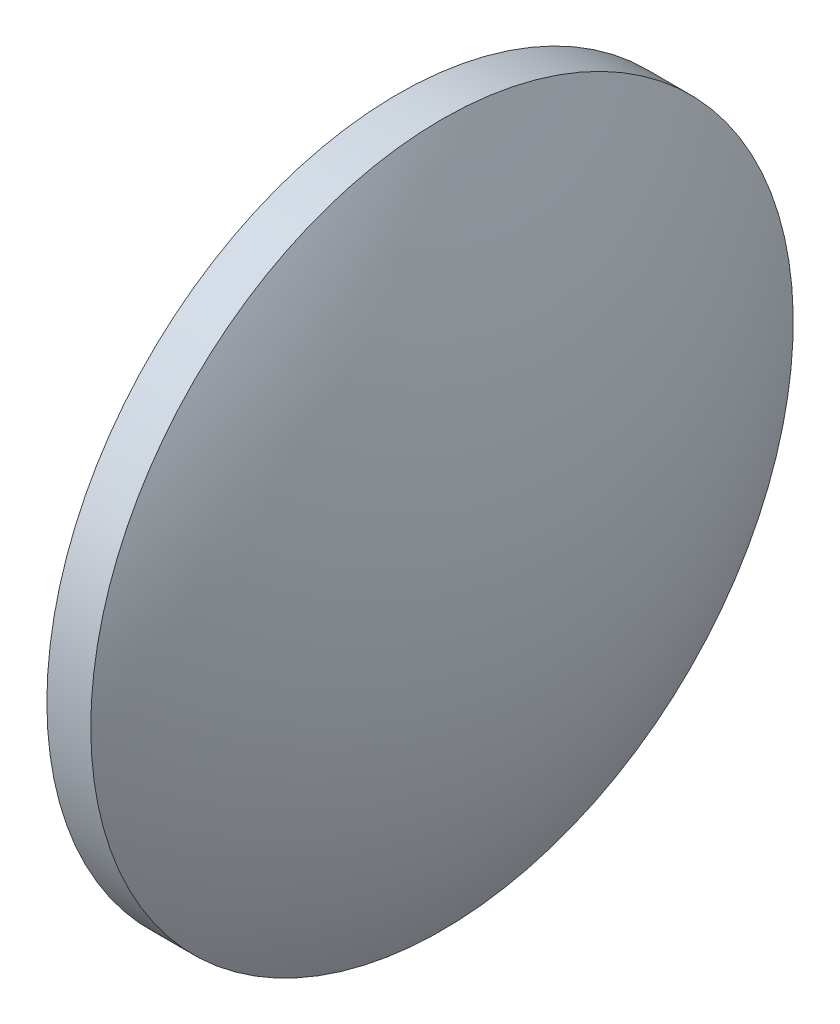
SolidWorks part; units mm, degrees
ref_plane "前视基准面" through (0, 0, 0) normal (0, 0, 1) x (1, 0, 0)
ref_plane "上视基准面" through (0, 0, 0) normal (0, 1, 0) x (1, 0, 0)
ref_plane "右视基准面" through (0, 0, 0) normal (1, 0, 0) x (0, 0, -1)
sketch "草图2" plane through (0, 0, 0) normal (0, 0, 1) x (1, 0, 0)
  line L0 (442.6491, 15.686) -> (461.8253, 15.686) construction
  line L1 (447.3437, 15.686) -> (447.3437, 35.686)
  line L2 (455.0137, 15.686) -> (447.3437, 15.686)
  line L5 (449.8437, 35.686) -> (447.3437, 35.686)
  arc A0 (455.0137, 15.686) -> (449.8437, 35.686) centre (413.744, 15.686) ccw
revolve "旋转2" add sketch "草图2" angle 360 about L0
